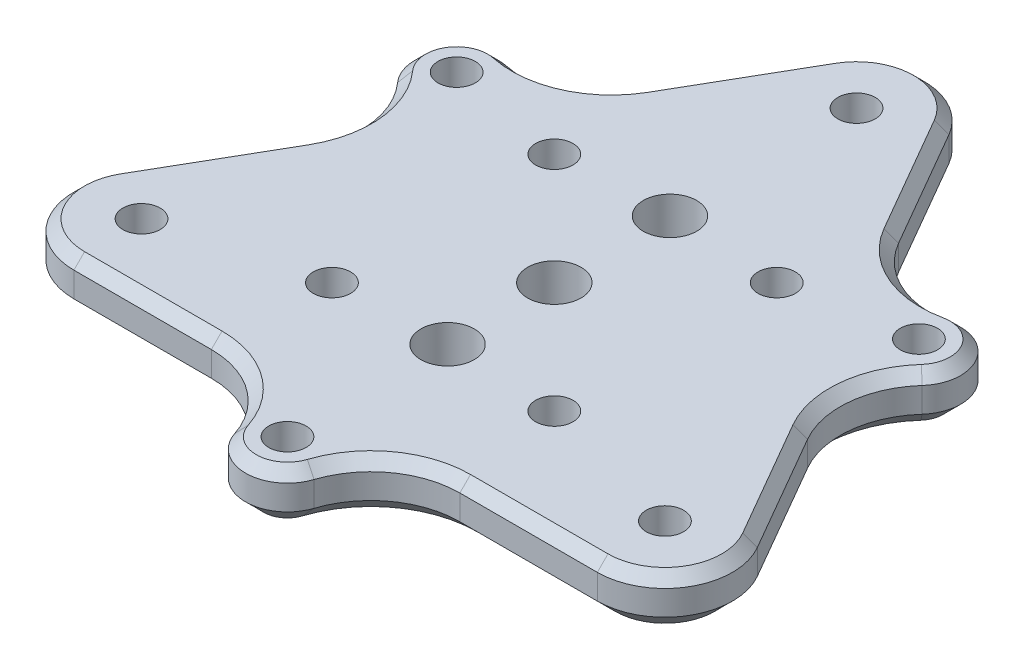
SolidWorks part; units mm, degrees
material "5052-O"
ref_plane "正面" through (0, 0, 0) normal (0, 0, 1) x (1, 0, 0)
ref_plane "平面" through (0, 0, 0) normal (0, 1, 0) x (1, 0, 0)
ref_plane "右側面" through (0, 0, 0) normal (1, 0, 0) x (0, 0, -1)
sketch "ｽｹｯﾁ1" plane through (0, 0, 0) normal (0, 1, 0) x (1, 0, 0)
  line L1 (-28.3308, 10.9297) -> (-23.6409, 8.222)
  line L2 (4.7, -30) -> (4.7, -24.5846)
  line L3 (-23.6308, 19.0703) -> (-18.9409, 16.3626)
  line L4 (28.3308, 10.9297) -> (23.6409, 8.222)
  line L5 (-4.7, -30) -> (-4.7, -24.5846)
  line L8 (23.6308, 19.0703) -> (18.9409, 16.3626)
  line L17 (-36, -13.1846) -> (-6.5818, 37.7692)
  line L20 (29.4182, -24.5846) -> (-29.4182, -24.5846)
  line L23 (6.5818, 37.7692) -> (36, -13.1846)
  line L24 (36, -13.1846) -> (35.8926, -13.3525)
  circle A2 centre (25.9808, 15) radius 2.1
  circle A3 centre (-25.9808, 15) radius 2.1
  circle A4 centre (0, -30) radius 2.1
  circle A5 centre (29.4182, -16.9846) radius 7.6
  circle A6 centre (29.4182, -16.9846) radius 5
  circle A7 centre (-29.4182, -16.9846) radius 7.6
  circle A8 centre (25.9808, 15) radius 4.7
  circle A9 centre (-25.9808, 15) radius 4.7
  circle A10 centre (0, -30) radius 4.7
  circle A11 centre (-29.4182, -16.9846) radius 5
  circle A12 centre (0, 33.9692) radius 7.6
  circle A13 centre (0, 33.9692) radius 5
extrude "ﾎﾞｽ - 押し出し1" add sketch "ｽｹｯﾁ1" along normal blind 6
fillet "ﾌｨﾚｯﾄ1" radius 10 6 edges at (-23.6409, 3, -8.222) (-18.9409, 3, -16.3626) (18.9409, 3, -16.3626) (23.6409, 3, -8.222) (4.7, 3, 24.5846) (-4.7, 3, 24.5846)
chamfer "面取り1" distance 1.2 angle 45 18 edges at (36, 6, 20.7846) (21.6925, 6, 24.5846) (32.1371, 6, 6.494) (26.9878, 6, -6.227) (30.0511, 6, -17.35) (18.8866, 6, -20.2586) (10.4446, 6, -31.0786) (0, 6, -41.5692) (-10.4446, 6, -31.0786) (-18.8866, 6, -20.2586) (-30.0511, 6, -17.35) (-26.9878, 6, -6.227) (-32.1371, 6, 6.494) (-36, 6, 20.7846) (-21.6925, 6, 24.5846) (-8.1011, 6, 26.4856) (0, 6, 34.7) (8.1011, 6, 26.4856)
chamfer "面取り3" distance 2 angle 45 18 edges at (-18.8866, 0, -20.2586) (-10.4446, 0, -31.0786) (0, 0, -41.5692) (10.4446, 0, -31.0786) (18.8866, 0, -20.2586) (30.0511, 0, -17.35) (26.9878, 0, -6.227) (32.1371, 0, 6.494) (36, 0, 20.7846) (21.6925, 0, 24.5846) (8.1011, 0, 26.4856) (0, 0, 34.7) (-8.1011, 0, 26.4856) (-21.6925, 0, 24.5846) (-36, 0, 20.7846) (-32.1371, 0, 6.494) (-26.9878, 0, -6.227) (-30.0511, 0, -17.35)
sketch "ｽｹｯﾁ3" plane through (0, 0, 0) normal (0, -1, 0) x (1, 0, 0)
  circle A0 centre (0, 0) radius 3
extrude "ｶｯﾄ - 押し出し4" cut sketch "ｽｹｯﾁ3" against normal blind 15
sketch "ｽｹｯﾁ4" plane through (0, 0, 0) normal (0, -1, 0) x (1, 0, 0)
  circle A0 centre (0, 12.5) radius 3
  circle A1 centre (0, -12.5) radius 3
  circle A2 centre (-12.5, 12.5) radius 5
  circle A3 centre (12.5, 12.5) radius 5
  circle A4 centre (12.5, -12.5) radius 5
  circle A5 centre (-12.5, -12.5) radius 5
  circle A6 centre (-12.5, 12.5) radius 2.1
  circle A7 centre (12.5, 12.5) radius 2.1
  circle A8 centre (12.5, -12.5) radius 2.1
  circle A9 centre (-12.5, -12.5) radius 2.1
extrude "ｶｯﾄ - 押し出し9" cut sketch "ｽｹｯﾁ4" against normal blind 2 contours A4 | A5 | A2 | A3
sketch "ｽｹｯﾁ5" plane through (0, 2, 0) normal (0, -1, 0) x (1, 0, 0)
  circle A0 centre (12.5, 12.5) radius 2.1
  circle A1 centre (-12.5, 12.5) radius 2.1
  circle A2 centre (-12.5, -12.5) radius 2.1
  circle A3 centre (12.5, -12.5) radius 2.1
extrude "ｶｯﾄ - 押し出し11" cut sketch "ｽｹｯﾁ5" against normal up to next
sketch "ｽｹｯﾁ6" plane through (0, 0, 0) normal (0, -1, 0) x (-1, 0, 0)
  circle A0 centre (0, 13) radius 3
  circle A1 centre (0, -12) radius 3
extrude "ｶｯﾄ - 押し出し12" cut sketch "ｽｹｯﾁ6" against normal up to next
chamfer "面取り4" distance 0.25 angle 45 4 edges at (12.5, 0, 7.5) (12.5, 0, -17.5) (-12.5, 0, -17.5) (-12.5, 0, 7.5)
sketch "ｽｹｯﾁ8" plane through (0, 6, 0) normal (0, 1, 0) x (1, 0, 0)
  circle A0 centre (29.4182, -16.9846) radius 5
  circle A1 centre (29.4182, -16.9846) radius 2.1
extrude "ﾎﾞｽ - 押し出し4" add sketch "ｽｹｯﾁ8" against normal blind 4
sketch "ｽｹｯﾁ9" plane through (0, 6, 0) normal (0, 1, 0) x (1, 0, 0)
  circle A0 centre (0, 33.9692) radius 5
  circle A1 centre (0, 33.9692) radius 2.1
  circle A2 centre (-29.4182, -16.9846) radius 5
  circle A3 centre (-29.4182, -16.9846) radius 2.1
extrude "ﾎﾞｽ - 押し出し5" add sketch "ｽｹｯﾁ9" against normal blind 4
